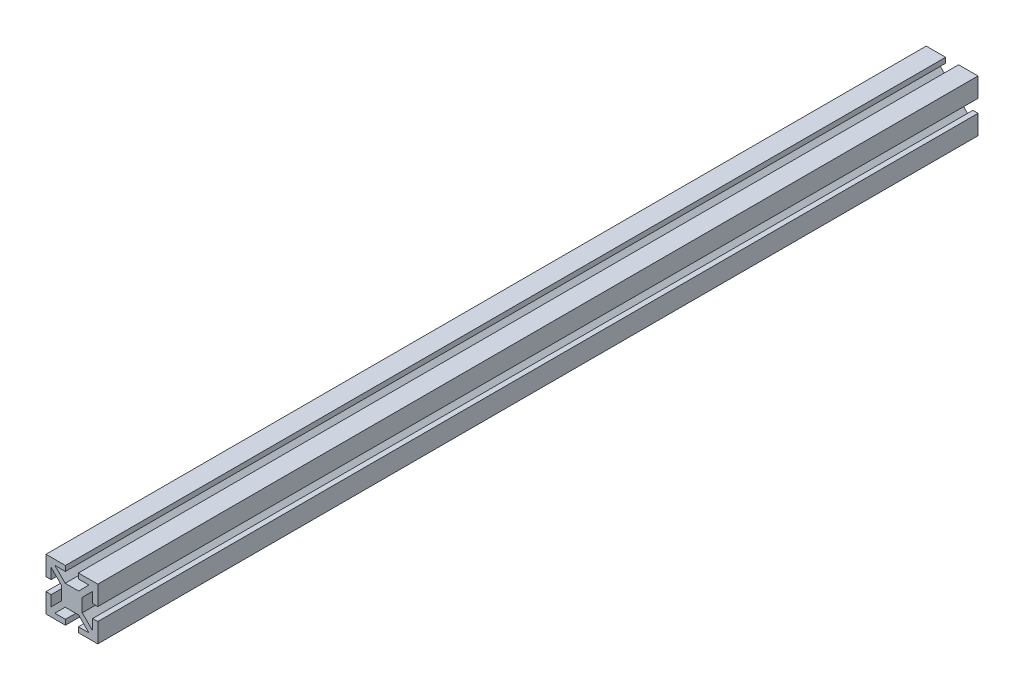
SolidWorks part; units mm, degrees
ref_plane "Front Plane" through (0, 0, 0) normal (0, 0, 1) x (1, 0, 0)
ref_plane "Top Plane" through (0, 0, 0) normal (0, 1, 0) x (1, 0, 0)
ref_plane "Right Plane" through (0, 0, 0) normal (1, 0, 0) x (0, 0, -1)
sketch "Sketch1" plane through (0, 0, 0) normal (0, 0, 1) x (1, 0, 0)
  line L0 (0, 4) -> (0, -4) construction
  line L1 (-2.5858, 4) -> (2.5858, 4)
  line L2 (-4, 2.5858) -> (-4, -2.5858)
  line L5 (-10, 10) -> (0, 0) construction
  line L6 (0, 10) -> (0, 4) construction
  line L7 (-4, 2.5858) -> (-8, 6.5858)
  line L8 (-6.5858, 8) -> (-2.5, 8)
  line L9 (-2.5, 8) -> (-2.5, 10)
  line L10 (-2.5, 10) -> (-10, 10)
  line L11 (-10, 10) -> (-10, 2.5)
  line L12 (-10, 2.5) -> (-8, 2.5)
  line L13 (-8, 2.5) -> (-8, 6.5858)
  line L14 (-4, 0) -> (4, 0) construction
  line L15 (-4, 0) -> (-10, 0) construction
  line L16 (-2.5858, 4) -> (-6.5858, 8)
  line L17 (-10, -10) -> (0, 0) construction
  line L18 (-2.5858, -4) -> (-6.5858, -8)
  line L19 (-8, -2.5) -> (-8, -6.5858)
  line L20 (-10, -2.5) -> (-8, -2.5)
  line L21 (-10, -10) -> (-10, -2.5)
  line L22 (-2.5, -10) -> (-10, -10)
  line L23 (-2.5, -8) -> (-2.5, -10)
  line L24 (-6.5858, -8) -> (-2.5, -8)
  line L25 (-4, -2.5858) -> (-8, -6.5858)
  line L26 (-2.5858, -4) -> (2.5858, -4)
  line L27 (10, -10) -> (0, 0) construction
  line L28 (4, 0) -> (10, 0) construction
  line L29 (10, 10) -> (0, 0) construction
  line L30 (4, -2.5858) -> (8, -6.5858)
  line L31 (6.5858, -8) -> (2.5, -8)
  line L32 (2.5, -8) -> (2.5, -10)
  line L33 (2.5, -10) -> (10, -10)
  line L34 (10, -10) -> (10, -2.5)
  line L35 (10, -2.5) -> (8, -2.5)
  line L36 (8, -2.5) -> (8, -6.5858)
  line L37 (2.5858, -4) -> (6.5858, -8)
  line L38 (2.5858, 4) -> (6.5858, 8)
  line L39 (8, 2.5) -> (8, 6.5858)
  line L40 (10, 2.5) -> (8, 2.5)
  line L41 (10, 10) -> (10, 2.5)
  line L42 (2.5, 10) -> (10, 10)
  line L43 (2.5, 8) -> (2.5, 10)
  line L44 (6.5858, 8) -> (2.5, 8)
  line L45 (4, 2.5858) -> (8, 6.5858)
  line L46 (4, 2.5858) -> (4, -2.5858)
  point P0 (0, 0)
  dimension "D1" = 10
  dimension "D2" = 4
  dimension "D3" = 2
  dimension "D4" = 10
  dimension "D5" = 2
  dimension "D6" = 2.5
  dimension "D7" = 2.5
  dimension "D8" = 4
  dimension "D9" = 1
  dimension "D10" = 1
extrude "Boss-Extrude1" add sketch "Sketch1" along normal mid plane 340
